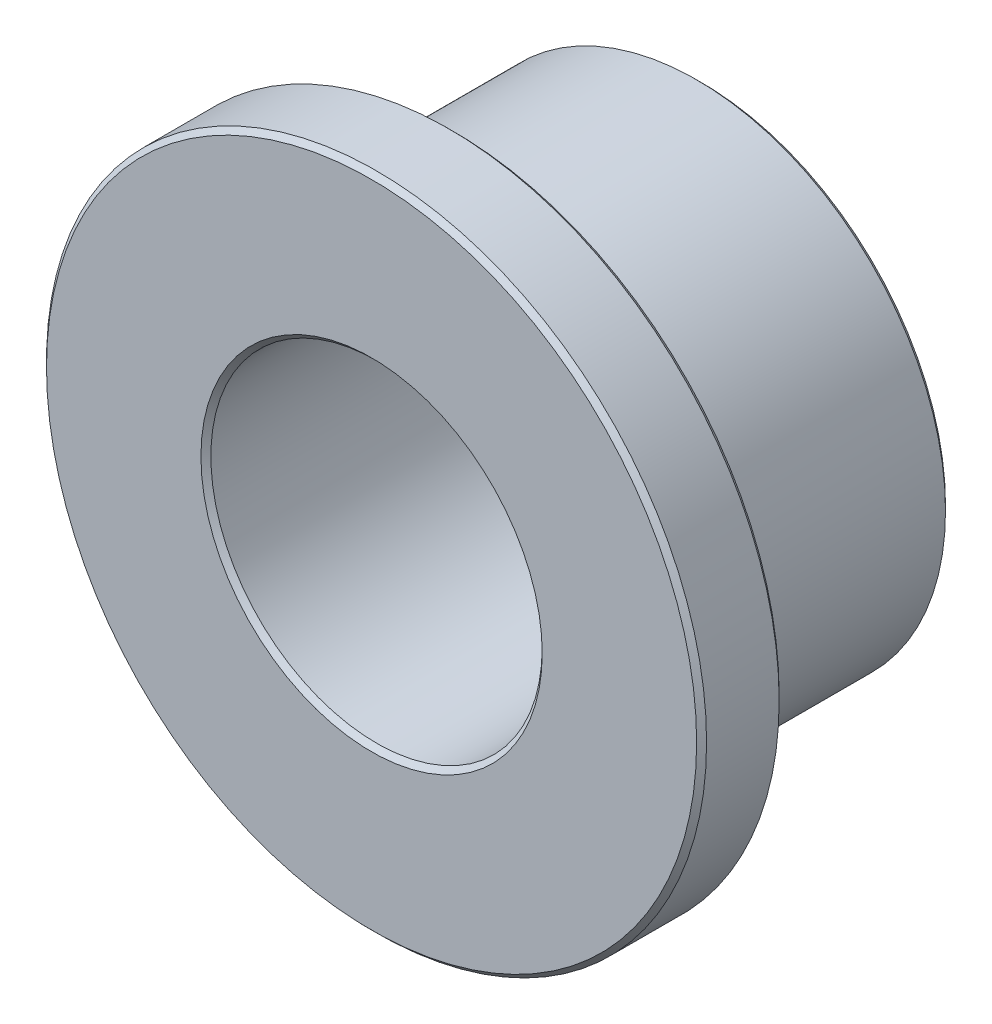
SolidWorks part; units mm, degrees
ref_plane "Front" through (0, 0, 0) normal (0, 0, 1) x (1, 0, 0)
ref_plane "Top" through (0, 0, 0) normal (0, 1, 0) x (1, 0, 0)
ref_plane "Right" through (0, 0, 0) normal (1, 0, 0) x (0, 0, -1)
sketch "Sketch1" plane through (0, 0, 0) normal (0, 0, 1) x (1, 0, 0)
  circle A0 centre (0, 0) radius 3.1877
  circle A1 centre (0, 0) radius 4.7879
  circle A2 centre (0, 0) radius 6.35
  dimension "ID" = 6.3754
  dimension "OD" = 9.5758
  dimension "Flange OD" = 12.7
sketch "Sketch2" plane through (0, 0, 0) normal (1, 0, 0) x (0, 0, -1)
  line L0 (-3.175, -6.35) -> (3.175, -6.35) construction
  line L1 (0, 6.35) -> (0, -6.35) construction
  line L3 (-1.5875, 4.7879) -> (3.175, 4.7879) construction
  point P3 (0, -6.35)
  point P7 (0, 4.7879)
  point P9 (-1.5875, -6.35)
  point P10 (-3.175, 6.35)
  point P23 (0, 6.35)
  dimension "Flange Thickness" = 1.5875
  dimension "Length" = 6.35
sketch "Sketch3" plane through (0, 0, 0) normal (0, 0, 1) x (1, 0, 0)
  circle A0 centre (0, 0) radius 6.35 construction
  circle A1 centre (0, 0) radius 6.35
  circle A2 centre (0, 0) radius 3.1877 construction
  circle A3 centre (0, 0) radius 3.1877
extrude "Boss-Extrude1" add sketch "Sketch3" against normal up to vertex (-1.5875 mm away) from vertex at 3.175 starting at point (0, -6.35, 3.175)
sketch "Sketch4" plane through (0, 0, 0) normal (0, 0, 1) x (1, 0, 0)
  circle A0 centre (0, 0) radius 3.1877 construction
  circle A1 centre (0, 0) radius 4.7879 construction
  circle A2 centre (0, 0) radius 3.1877
  circle A3 centre (0, 0) radius 4.7879
extrude "Boss-Extrude2" add sketch "Sketch4" against normal up to vertex (3.175 mm away) from vertex at 1.5875 starting at point (0, -6.35, 1.5875)
chamfer "Chamfer1" distance 0.0956 angle 45 6 edges at (3.1877, 0, 3.175) (6.35, 0, 3.175) (6.35, 0, 1.5875) (4.7879, 0, 1.5875) (3.1877, 0, -3.175) (4.7879, 0, -3.175)
equation "\"D1@Chamfer1\"=\"ID@Sketch1\"*0.015"
